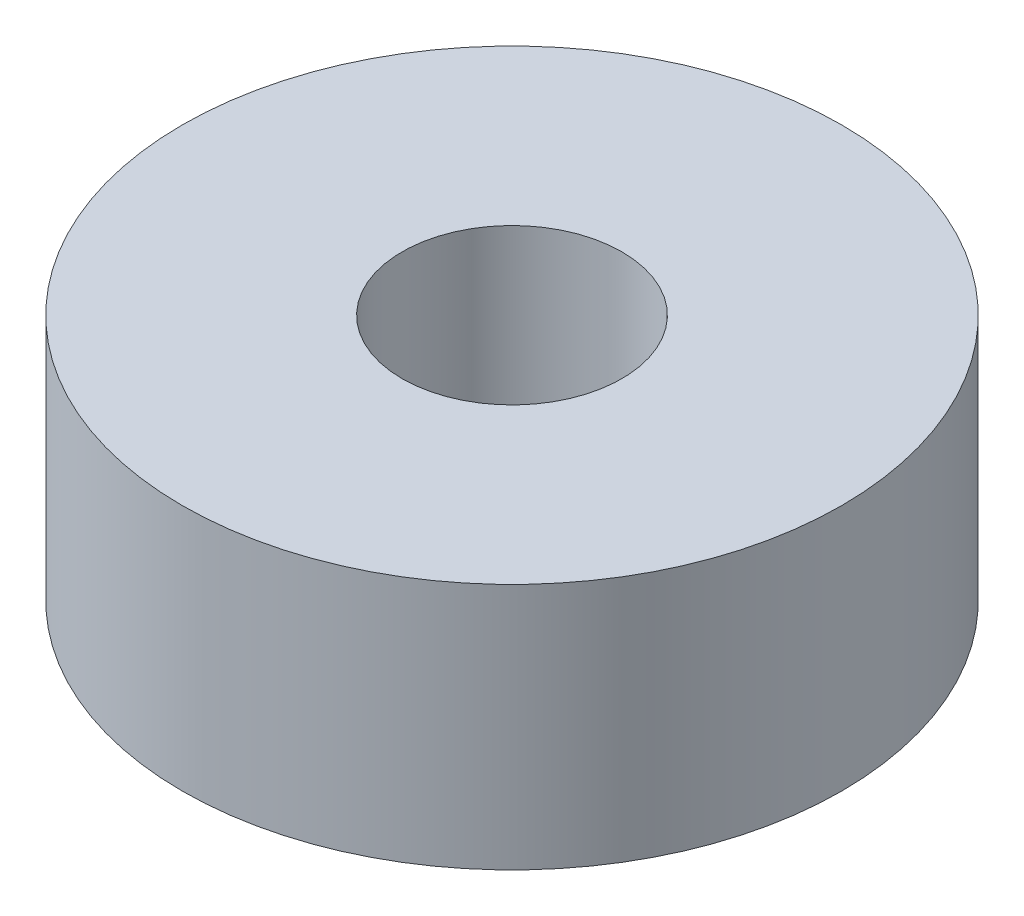
SolidWorks part; units mm, degrees
material "6063-T6"
ref_plane "Alzado" through (0, 0, 0) normal (0, 0, 1) x (1, 0, 0)
ref_plane "Planta" through (0, 0, 0) normal (0, 1, 0) x (1, 0, 0)
ref_plane "Vista lateral" through (0, 0, 0) normal (1, 0, 0) x (0, 0, -1)
sketch "Croquis1" plane through (0, 0, 0) normal (0, 1, 0) x (1, 0, 0)
  circle A0 centre (0, 0) radius 12
  circle A1 centre (0, 0) radius 4
  dimension "D1" = 8
  dimension "D2" = 24
extrude "Saliente-Extruir1" add sketch "Croquis1" along normal blind 9
